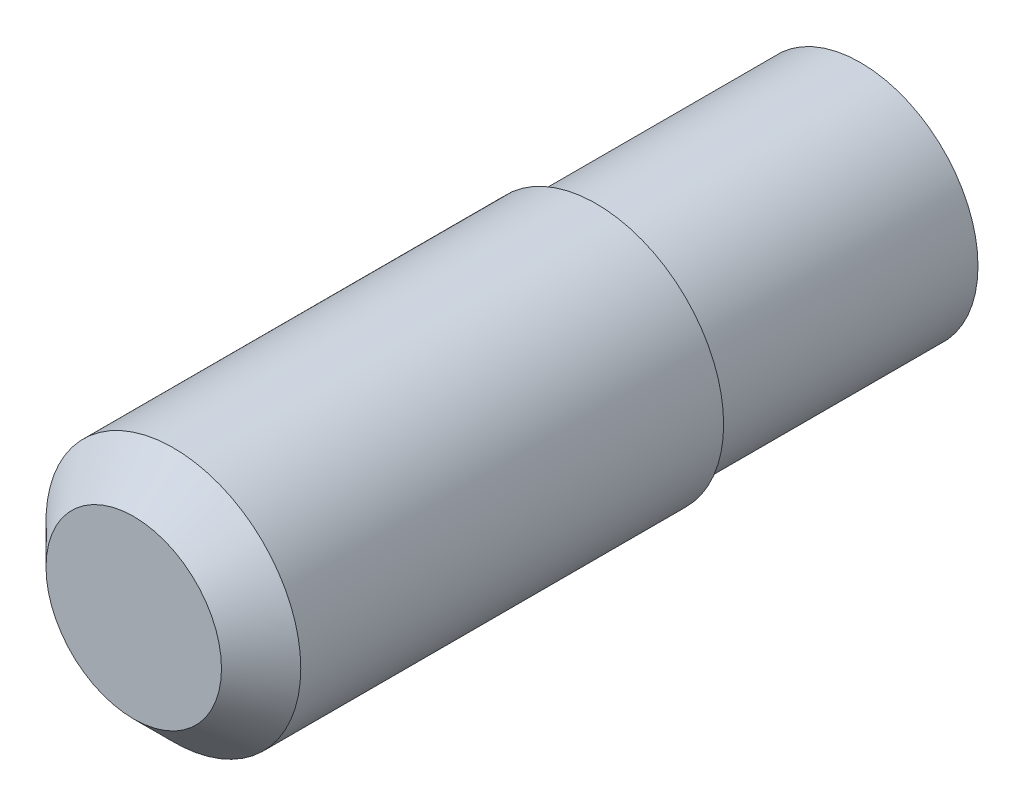
SolidWorks part; units mm, degrees
ref_plane "Front Plane" through (0, 0, 0) normal (0, 0, 1) x (1, 0, 0)
ref_plane "Top Plane" through (0, 0, 0) normal (0, 1, 0) x (1, 0, 0)
ref_plane "Right Plane" through (0, 0, 0) normal (1, 0, 0) x (0, 0, -1)
sketch "Sketch1" plane through (0, 0, 0) normal (0, 0, 1) x (1, 0, 0)
  circle A0 centre (137.1578, 37.1713) radius 5.9267
  dimension "D1" = 11.8533
extrude "Boss-Extrude1" add sketch "Sketch1" along normal blind 13.3333
sketch "Sketch2" plane through (0, 0, 13.3333) normal (0, 0, 1) x (1, 0, 0)
  circle A2 centre (137.1578, 37.1713) radius 6.4267
  circle A3 centre (137.1578, 37.1713) radius 6.4267
  dimension "D1" = 0.5
extrude "Boss-Extrude2" add sketch "Sketch2" along normal blind 16.6667
sketch "Sketch3" plane through (0, 0, 30) normal (0, 0, 1) x (1, 0, 0)
  circle A1 centre (137.1578, 37.1713) radius 6.4267
  circle A2 centre (137.1578, 37.1713) radius 6.4267
  dimension "D1" = 0
extrude "Boss-Extrude3" add sketch "Sketch3" along normal blind 6.6667
chamfer "Chamfer1" distance 2 angle 45 1 edges at (143.5845, 37.1713, 36.6667)
